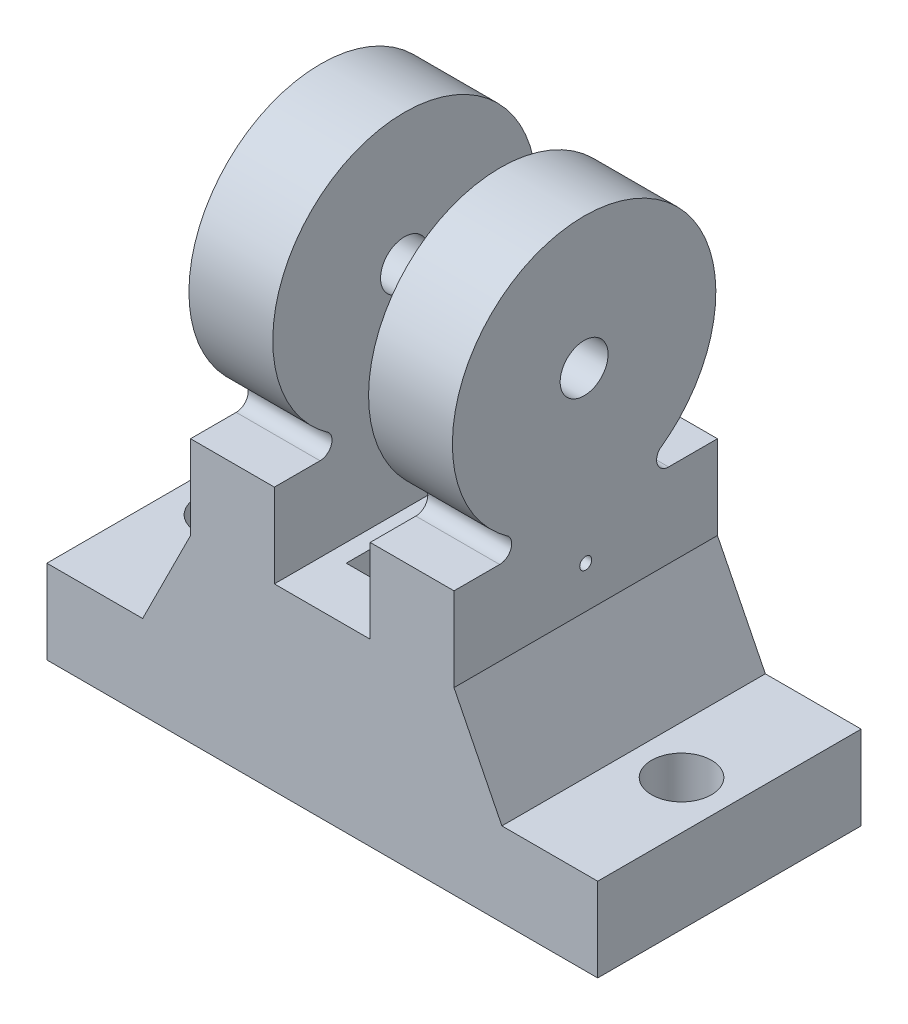
SolidWorks part; units mm, degrees
ref_plane "Front Plane" through (0, 0, 0) normal (0, 0, 1) x (1, 0, 0)
ref_plane "Top Plane" through (0, 0, 0) normal (0, 1, 0) x (1, 0, 0)
ref_plane "Right Plane" through (0, 0, 0) normal (1, 0, 0) x (0, 0, -1)
sketch "Sketch1" plane through (0, 0, 0) normal (0, 1, 0) x (1, 0, 0)
  line L0 (0, 11) -> (0, -11) construction
  line L1 (-11, 11) -> (11, 11)
  line L2 (-11, 11) -> (-11, -11)
  line L3 (-11, -11) -> (11, -11)
  line L4 (11, 11) -> (11, -11)
  line L5 (-11, 0) -> (11, 0) construction
  point P9 (0, 0)
  dimension "D1" = 22
extrude "Body Base" add sketch "Sketch1" along normal blind 20
sketch "Sketch8" plane through (0, 0, 0) normal (1, 0, 0) x (0, 0, -1)
  line L1 (-11, 20) -> (11, 20)
  line L2 (-11, 20) -> (-11, 15)
  line L3 (-11, 15) -> (11, 15)
  line L4 (11, 20) -> (11, 15)
  dimension "D1" = 22
  dimension "D2" = 5
extrude "Channel for Tendons" cut sketch "Sketch8" against normal mid plane 8
sketch "Sketch9" plane through (11, 0, 0) normal (1, 0, 0) x (0, 0, -1)
  line L0 (-11, 20) -> (-11, 22)
  line L1 (-11, 22) -> (-7.1883, 22)
  line L2 (-11, 20) -> (11, 20)
  line L3 (0, 11) -> (0, -11) construction
  line L4 (11, 20) -> (11, 22)
  line L6 (11, 22) -> (6.9193, 22)
  arc A2 (-7.1883, 22) -> (-6.4317, 23.6538) centre (-7.1883, 23) ccw
  arc A3 (6.1627, 23.6538) -> (6.9193, 22) centre (6.9193, 23) ccw
  arc A4 (6.1627, 23.6538) -> (-6.4317, 23.6538) centre (-0.1345, 32.673) ccw
  point P12 (-4.5, 22)
  point P15 (4.5, 22)
  dimension "D3" = 1
  dimension "D1" = 6.5
  dimension "D2" = 2
extrude "Boss-Extrude2" add sketch "Sketch9" against normal blind 7
pattern_linear "LPattern1" count 2 spacing 15 along (-1, 0, 0) of "Boss-Extrude2"
sketch "Sketch11" plane through (11, 0, 0) normal (1, 0, 0) x (0, 0, -1)
  line L1 (-0.1345, 32.673) -> (-2.5336, 32.673) construction
  circle A2 centre (-0.1345, 32.673) radius 2
extrude "Connect to Grippers" cut sketch "Sketch11" against normal through all
sketch "Sketch12" plane through (0, 0, 0) normal (0, 0, 1) x (1, 0, 0)
  line L0 (-11, 11) -> (11, 11) construction
  line L1 (-11, 22) -> (-11, 0) construction
  line L2 (11, 22) -> (11, 0) construction
  line L3 (-4, 15) -> (-11, 15) construction
  line L4 (-11, 15) -> (-15, 7)
  line L5 (-15, 7) -> (-23, 7)
  line L6 (-23, 7) -> (-23, 0)
  line L7 (0, -12.174) -> (0, 12.174) construction
  line L8 (11, 15) -> (15, 7)
  line L9 (23, 7) -> (23, 0)
  line L10 (15, 7) -> (23, 7)
  line L11 (-23, 0) -> (-11, 0)
  line L12 (12.1, 0) -> (-12.1, 0) construction
  line L13 (-11, 0) -> (-11, 15)
  line L14 (23, 0) -> (11, 0)
  line L15 (11, 0) -> (11, 15)
  dimension "D1" = 8
  dimension "D2" = 8
  dimension "D3" = 12
extrude "Boss-Extrude3" add sketch "Sketch12" along normal mid plane 22
sketch "Sketch13" plane through (0, 7, 0) normal (0, 1, 0) x (1, 0, 0)
  line L0 (-19, 11) -> (-19, -11) construction
  line L1 (-15, 11) -> (-23, 11) construction
  line L2 (-15, -11) -> (-23, -11) construction
  line L3 (19, 11) -> (19, -11) construction
  line L4 (23, 11) -> (15, 11) construction
  line L5 (23, -11) -> (15, -11) construction
  line L6 (0, -12.174) -> (0, 12.174) construction
  circle A0 centre (-19, 0) radius 2.5
  circle A1 centre (19, 0) radius 2.5
extrude "Cut-Extrude3" cut sketch "Sketch13" against normal through all
sketch "Sketch16" plane through (0, 15, 0) normal (0, 1, 0) x (1, 0, 0)
  line L0 (-4, 0) -> (4, 0) construction
  line L1 (-4, -11) -> (-4, 11) construction
  line L3 (0, 0) -> (0, 3.3191) construction
  line L4 (0, -12.174) -> (0, 12.174) construction
  line L6 (-2.5, -6.5) -> (2.5, -6.5)
  line L7 (-2.5, -6.5) -> (-2.5, 6.5)
  line L8 (-2.5, 6.5) -> (2.5, 6.5)
  line L9 (2.5, -6.5) -> (2.5, 6.5)
  line L10 (-2.5, -6.5) -> (2.5, 6.5) construction
  line L11 (-2.5, 6.5) -> (2.5, -6.5) construction
  dimension "D1" = 5
  dimension "D2" = 13
extrude "Tendon Pass Through Hole" cut sketch "Sketch16" against normal through all
sketch "Sketch17" plane through (-11, 0, 0) normal (-1, 0, 0) x (0, 0, 1)
  line L0 (11, 18.5) -> (-11, 18.5) construction
  line L1 (11, 22) -> (11, 15) construction
  line L2 (-11, 22) -> (-11, 15) construction
  line L3 (0, 18.5) -> (0, 16.7772) construction
  line L4 (0, -12.1) -> (0, 12.1) construction
  circle A0 centre (0, 18.5) radius 0.5
  dimension "D1" = 1
extrude "Tendon Pin Hole" cut sketch "Sketch17" against normal through all
